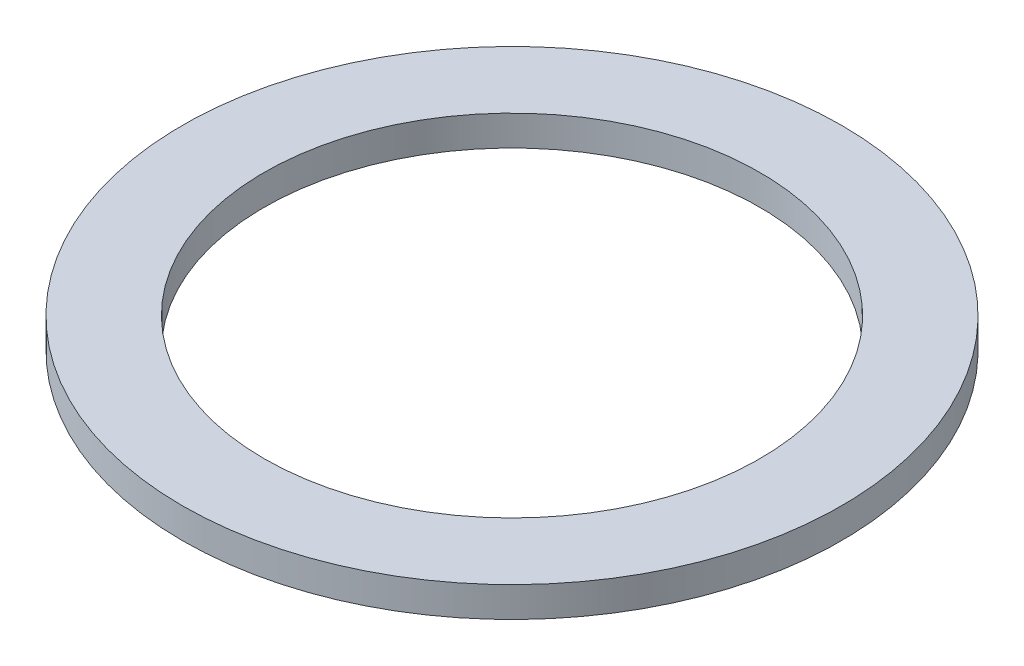
SolidWorks part; units mm, degrees
ref_plane "Front Plane" through (0, 0, 0) normal (0, 0, 1) x (1, 0, 0)
ref_plane "Top Plane" through (0, 0, 0) normal (0, 1, 0) x (1, 0, 0)
ref_plane "Right Plane" through (0, 0, 0) normal (1, 0, 0) x (0, 0, -1)
sketch "Sketch1" plane through (0, 0, 0) normal (0, 1, 0) x (1, 0, 0)
  circle A0 centre (0, 0) radius 5.45
  circle A1 centre (0, 0) radius 4.1
  dimension "D1" = 10.9
  dimension "D2" = 8.2
extrude "Boss-Extrude1" add sketch "Sketch1" along normal blind 0.5
